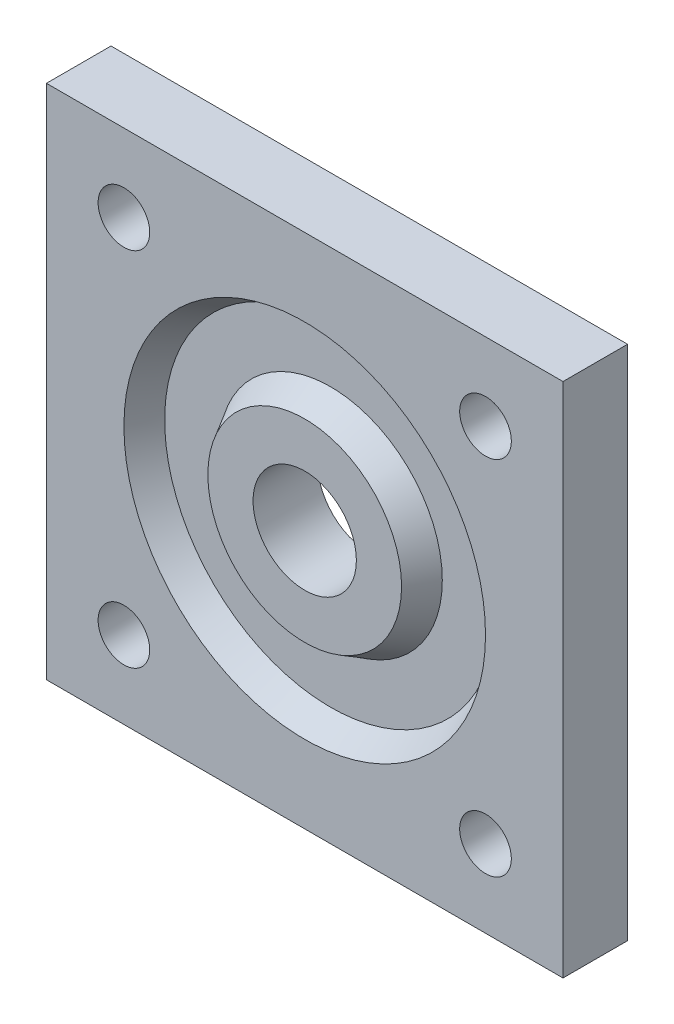
SolidWorks part; units mm, degrees
ref_plane "Front Plane" through (0, 0, 0) normal (0, 0, 1) x (1, 0, 0)
ref_plane "Top Plane" through (0, 0, 0) normal (0, 1, 0) x (1, 0, 0)
ref_plane "Right Plane" through (0, 0, 0) normal (1, 0, 0) x (0, 0, -1)
sketch "Sketch1" plane through (0, 0, 0) normal (0, 0, 1) x (1, 0, 0)
  line L1 (-20, -20) -> (20, -20)
  line L2 (-20, -20) -> (-20, 20)
  line L3 (-20, 20) -> (20, 20)
  line L4 (20, -20) -> (20, 20)
  line L5 (-20, -20) -> (20, 20) construction
  line L6 (-20, 20) -> (20, -20) construction
  point P0 (0, 0)
  dimension "D1" = 40
  dimension "D2" = 40
extrude "Boss-Extrude1" add sketch "Sketch1" along normal blind 5
sketch "Sketch2" plane through (0, 0, 5) normal (0, 0, 1) x (1, 0, 0)
  circle A0 centre (0, 0) radius 14
  circle A1 centre (0, 0) radius 7.5
  dimension "D1" = 28
  dimension "D2" = 15
extrude "Cut-Extrude1" cut sketch "Sketch2" against normal blind 2 draft 30
sketch "Sketch3" plane through (0, 0, 5) normal (0, 0, 1) x (1, 0, 0)
  circle A0 centre (0, 0) radius 4
  dimension "D1" = 8
extrude "Cut-Extrude2" cut sketch "Sketch3" against normal through all
sketch "Sketch4" plane through (0, 0, 5) normal (0, 0, 1) x (1, 0, 0)
  line L0 (20, 20) -> (-20, 20) construction
  line L1 (-20, 20) -> (-20, -20) construction
  circle A0 centre (-14, 14) radius 2
  circle A1 centre (14, 14) radius 2
  circle A2 centre (14, -14) radius 2
  circle A3 centre (-14, -14) radius 2
  point P15 (0, 0)
  dimension "D1" = 4
  dimension "D2" = 6
  dimension "D3" = 6
  dimension "D4" = 4
extrude "Cut-Extrude3" cut sketch "Sketch4" against normal through all
sketch "Sketch5" plane through (0, 0, 0) normal (0, 0, -1) x (-1, 0, 0)
  line L0 (-20, 0) -> (20, 0) construction
  line L1 (20, 20) -> (20, -20) construction
  point P7 (0, 0)
